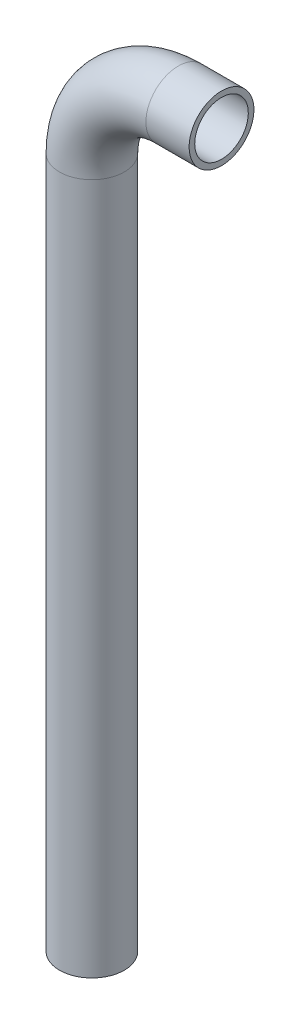
SolidWorks part; units mm, degrees
material "6061 Alloy"
ref_plane "Front Plane" through (0, 0, 0) normal (0, 0, 1) x (1, 0, 0)
ref_plane "Top Plane" through (0, 0, 0) normal (0, 1, 0) x (1, 0, 0)
ref_plane "Right Plane" through (0, 0, 0) normal (1, 0, 0) x (0, 0, -1)
sketch "Sketch1" plane through (0, 0, 0) normal (0, 1, 0) x (1, 0, 0)
  circle A0 centre (0, 0) radius 7.874
  circle A1 centre (0, 0) radius 9.525
  dimension "D1" = 19.05
  dimension "D2" = 1.651
sketch "Sketch2" plane through (0, 0, 0) normal (0, 0, 1) x (1, 0, 0)
  line L0 (0, 0) -> (0, 203.2)
  line L1 (25.4, 228.6) -> (38.1, 228.6)
  arc A0 (0, 203.2) -> (25.4, 228.6) centre (25.4, 203.2) cw
  dimension "D2" = 25.4
  dimension "D1" = 228.6
  dimension "D3" = 38.1
sweep "Sweep1" add profiles "Sketch1" path "Sketch2"
ref_plane "Plane1" through (0, 228.6, 0) normal (0, 1, 0) x (1, 0, 0)
